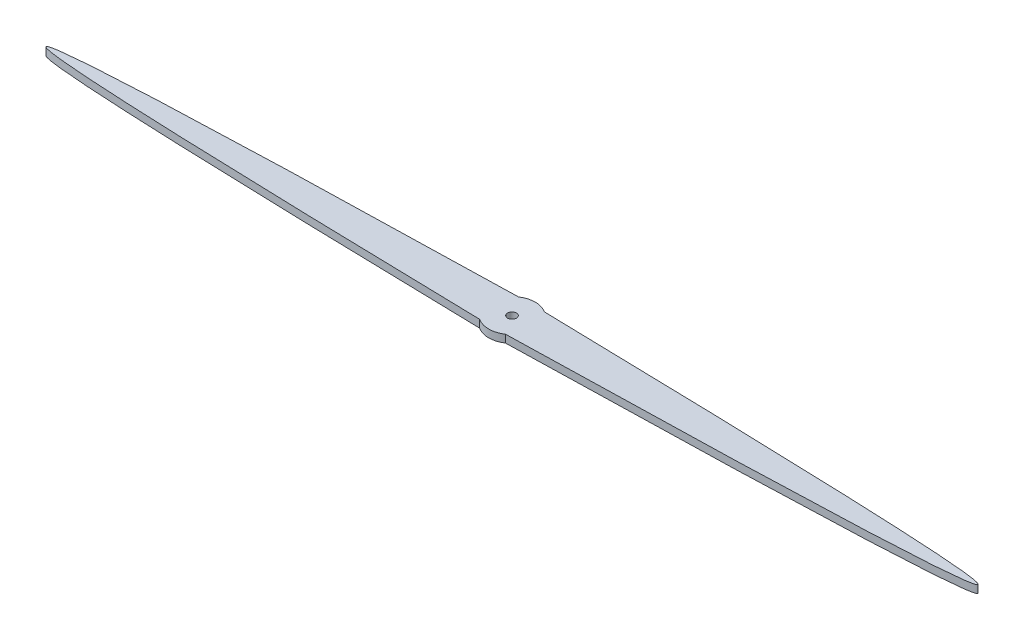
SolidWorks part; units mm, degrees
ref_plane "Front Plane" through (0, 0, 0) normal (0, 0, 1) x (1, 0, 0)
ref_plane "Top Plane" through (0, 0, 0) normal (0, 1, 0) x (1, 0, 0)
ref_plane "Right Plane" through (0, 0, 0) normal (1, 0, 0) x (0, 0, -1)
sketch "Sketch2" plane through (0, 0, 0) normal (0, 1, 0) x (1, 0, 0)
  line L0 (0, -3.508) -> (0, 5.9862) construction
  circle A0 centre (0, 0) radius 1.463
  arc A1 (-4.2121, -6.35) -> (4.2121, -6.35) centre (0, 0) ccw
  arc A2 (4.2121, 6.35) -> (-4.2121, 6.35) centre (0, 0) ccw
  spline S0 degree 2 poles (4.2121, 6.35) (300.5879, 0) (4.2121, -6.35) knots 0 0 0 1 1 1
  spline S1 degree 2 poles (-4.2121, 6.35) (-300.5879, 0) (-4.2121, -6.35) knots 0 0 0 1 1 1
  dimension "D1" = 2.9261
  dimension "D2" = 15.24
  dimension "D4" = 12.7
  dimension "D3" = 304.8
extrude "Boss-Extrude1" add sketch "Sketch2" along normal blind 2.5146
